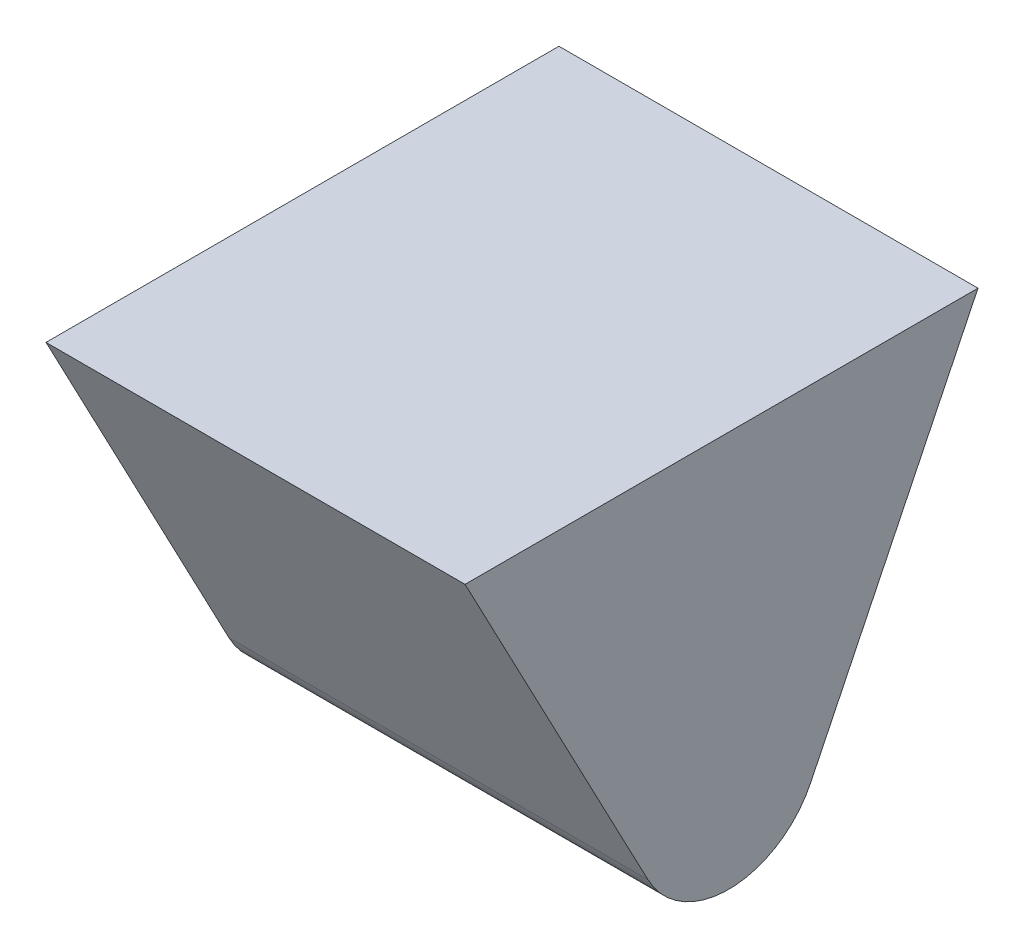
SolidWorks part; units mm, degrees
material "Glass"
ref_plane "Front Plane" through (0, 0, 0) normal (0, 0, 1) x (1, 0, 0)
ref_plane "Top Plane" through (0, 0, 0) normal (0, 1, 0) x (1, 0, 0)
ref_plane "Right Plane" through (0, 0, 0) normal (1, 0, 0) x (0, 0, -1)
sketch "Sketch1" plane through (0, 0, 0) normal (1, 0, 0) x (0, 0, -1)
  line L0 (-9.8603, 7.0641) -> (-2.7093, 7.0641)
  line L1 (-2.7093, 7.0641) -> (-6.139, 0)
  line L2 (-6.139, 0) -> (-9.8603, 7.0641)
  point P2 (-3.1357, 8.8551)
  point P4 (-9.2762, 5.9554)
  point P5 (-2.7093, 7.0641)
extrude "Boss-Extrude2" add sketch "Sketch1" along normal blind 5.842
fillet "Fillet2" radius 1.27 1 edges at (2.921, 0, 6.139)
